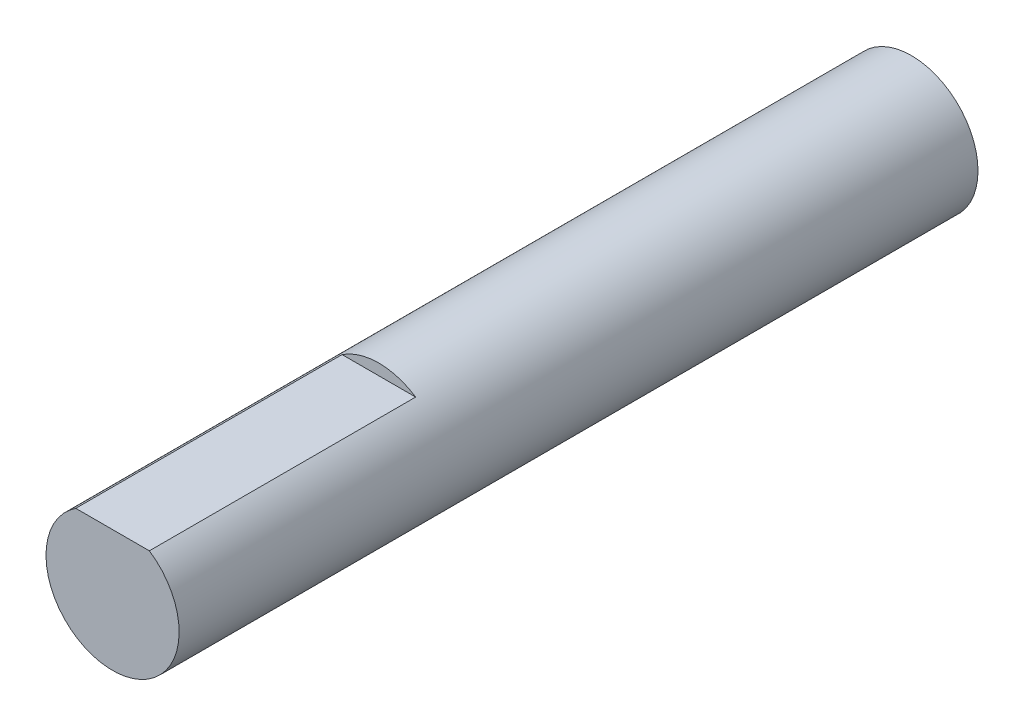
SolidWorks part; units mm, degrees
ref_plane "前视基准面" through (0, 0, 0) normal (0, 0, 1) x (1, 0, 0)
ref_plane "上视基准面" through (0, 0, 0) normal (0, 1, 0) x (1, 0, 0)
ref_plane "右视基准面" through (0, 0, 0) normal (1, 0, 0) x (0, 0, -1)
sketch "草图1" plane through (0, 0, 0) normal (0, 0, 1) x (1, 0, 0)
  circle A0 centre (0, 0) radius 3
  dimension "D1" = 6
extrude "凸台-拉伸1" add sketch "草图1" along normal blind 36 contours A0
sketch "草图2" plane through (0, 0, 36) normal (0, 0, 1) x (1, 0, 0)
  line L0 (-1.6583, 2.5) -> (1.6583, 2.5)
  arc A0 (1.6583, 2.5) -> (-1.6583, 2.5) centre (0, 0) ccw
  dimension "D1" = 6
  dimension "D2" = 2.5
extrude "切除-拉伸2" cut sketch "草图2" against normal blind 12
